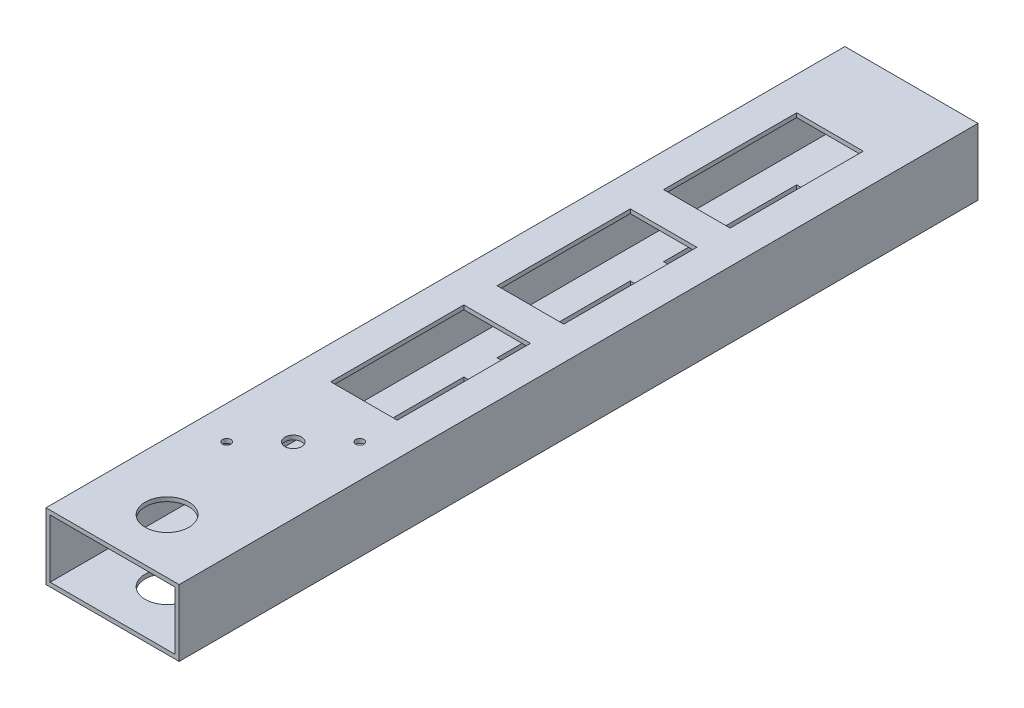
SolidWorks part; units mm, degrees
ref_plane "Front Plane" through (0, 0, 0) normal (0, 0, 1) x (1, 0, 0)
ref_plane "Top Plane" through (0, 0, 0) normal (0, 1, 0) x (1, 0, 0)
ref_plane "Right Plane" through (0, 0, 0) normal (1, 0, 0) x (0, 0, -1)
sketch "Sketch1" plane through (0, 0, 0) normal (0, 0, 1) x (1, 0, 0)
  line L1 (23.8125, -11.1125) -> (-23.8125, -11.1125)
  line L2 (23.8125, -11.1125) -> (23.8125, 11.1125)
  line L3 (23.8125, 11.1125) -> (-23.8125, 11.1125)
  line L4 (-23.8125, -11.1125) -> (-23.8125, 11.1125)
  line L5 (23.8125, -11.1125) -> (-23.8125, 11.1125) construction
  line L6 (23.8125, 11.1125) -> (-23.8125, -11.1125) construction
  line L7 (25.4, -12.7) -> (-25.4, -12.7)
  line L8 (25.4, -12.7) -> (25.4, 12.7)
  line L9 (25.4, 12.7) -> (-25.4, 12.7)
  line L10 (-25.4, -12.7) -> (-25.4, 12.7)
  line L11 (25.4, -12.7) -> (-25.4, 12.7) construction
  line L12 (25.4, 12.7) -> (-25.4, -12.7) construction
  point P0 (0, 0)
  point P6 (0, 0)
  dimension "D1" = 50.8
  dimension "D2" = 25.4
  dimension "D3" = 1.5875
  dimension "D4" = 1.5875
extrude "Boss-Extrude1" add sketch "Sketch1" along normal blind 304.8
sketch "Sketch3" plane through (0, 12.7, 0) normal (0, 1, 0) x (1, 0, 0)
  line L0 (0, 0) -> (0, -304.8) construction
  line L1 (25.4, 0) -> (-25.4, 0) construction
  line L2 (25.4, -304.8) -> (-25.4, -304.8) construction
  line L3 (12.7, -223.1575) -> (-12.7, -248.5575) construction
  line L5 (12.7, -158.07) -> (-12.7, -158.07)
  line L6 (12.7, -158.07) -> (12.7, -208.87)
  line L7 (12.7, -208.87) -> (-12.7, -208.87)
  line L8 (-12.7, -158.07) -> (-12.7, -208.87)
  line L9 (12.7, -158.07) -> (-12.7, -208.87) construction
  line L10 (12.7, -208.87) -> (-12.7, -158.07) construction
  line L11 (12.7, -94.57) -> (-12.7, -94.57)
  line L12 (12.7, -94.57) -> (12.7, -145.37)
  line L13 (12.7, -145.37) -> (-12.7, -145.37)
  line L14 (-12.7, -94.57) -> (-12.7, -145.37)
  line L15 (12.7, -94.57) -> (-12.7, -145.37) construction
  line L16 (12.7, -145.37) -> (-12.7, -94.57) construction
  line L17 (12.7, -31.07) -> (-12.7, -31.07)
  line L18 (12.7, -31.07) -> (12.7, -81.87)
  line L19 (12.7, -81.87) -> (-12.7, -81.87)
  line L20 (-12.7, -31.07) -> (-12.7, -81.87)
  line L21 (12.7, -31.07) -> (-12.7, -81.87) construction
  line L22 (12.7, -81.87) -> (-12.7, -31.07) construction
  circle A0 centre (0, -283.9996) radius 8.3469
  circle A1 centre (0, -235.8575) radius 3.175
  circle A2 centre (-12.7, -248.5575) radius 1.5875
  circle A3 centre (12.7, -223.1575) radius 1.5875
  point P13 (0, -235.8575)
  point P15 (0, -183.47)
  point P20 (0, -119.97)
  point P25 (0, -145.37)
  point P26 (0, -158.07)
  point P27 (12.7, -221.57)
  point P28 (0, -81.87)
  point P29 (0, -56.47)
  point P34 (0, -94.57)
  dimension "D2" = 3.175
  dimension "D3" = 6.35
  dimension "D7" = 12.7
  dimension "D1" = 25.4
  dimension "D4" = 25.4
  dimension "D5" = 50.8
  dimension "D6" = 12.7
  dimension "D8" = 12.7
extrude "Cut-Extrude2" cut sketch "Sketch3" against normal up to surface (25.4 mm away) up to face at (0, -12.7, 152.4)
